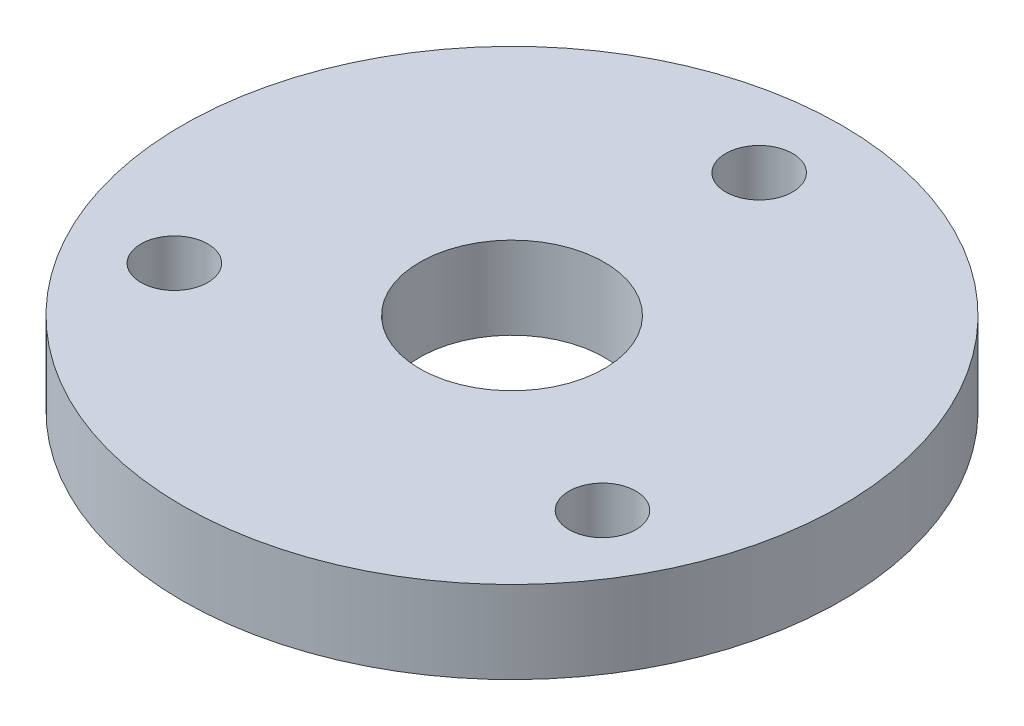
SolidWorks part; units mm, degrees
ref_plane "Front Plane" through (0, 0, 0) normal (0, 0, 1) x (1, 0, 0)
ref_plane "Top Plane" through (0, 0, 0) normal (0, 1, 0) x (1, 0, 0)
ref_plane "Right Plane" through (0, 0, 0) normal (1, 0, 0) x (0, 0, -1)
sketch "Sketch1" plane through (0, 0, 0) normal (0, 1, 0) x (1, 0, 0)
  circle A0 centre (0, 0) radius 100
  circle A1 centre (0, 0) radius 28
  circle A3 centre (0, 75) radius 10.15
  circle A4 centre (64.9519, -37.5) radius 10.15
  circle A5 centre (-64.9519, -37.5) radius 10.15
  point P14 (0, 0)
  dimension "D1" = 200
  dimension "D2" = 56
  dimension "D4" = 20.3
  dimension "D5" = 3
extrude "Boss-Extrude1" add sketch "Sketch1" along normal mid plane 25
